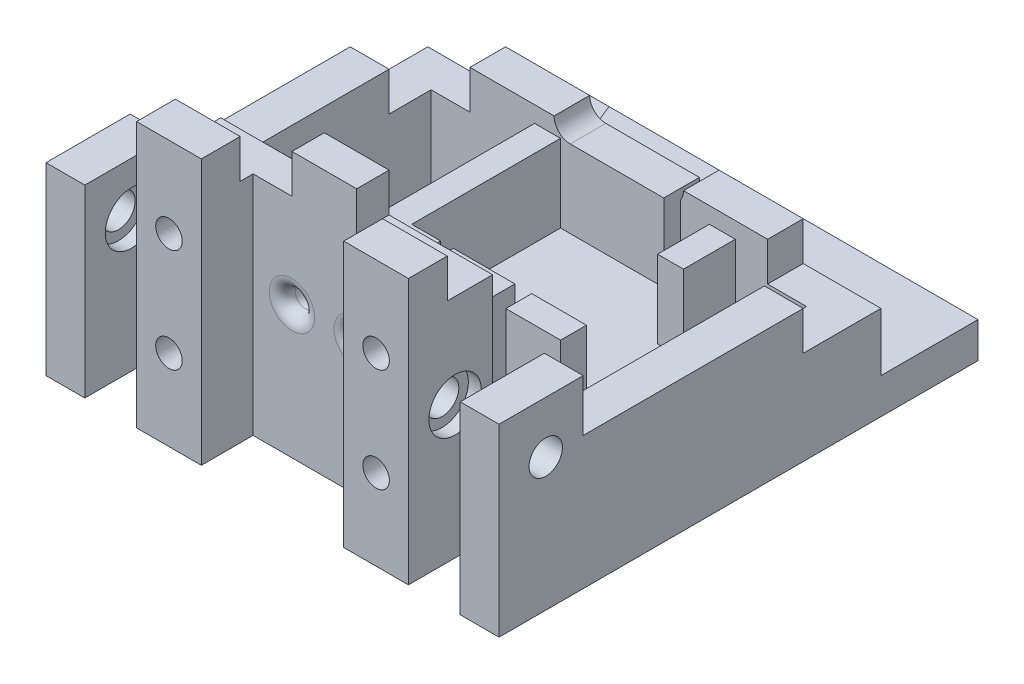
SolidWorks part; units mm, degrees
material "PBT General Purpose"
ref_plane "Front Plane" through (0, 0, 0) normal (0, 0, 1) x (1, 0, 0)
ref_plane "Top Plane" through (0, 0, 0) normal (0, 1, 0) x (1, 0, 0)
ref_plane "Right Plane" through (0, 0, 0) normal (1, 0, 0) x (0, 0, -1)
sketch "Sketch1" plane through (0, 0, 0) normal (0, 1, 0) x (1, 0, 0)
  line L0 (-29, 24) -> (-29, -29.5)
  line L1 (-35, 29.5) -> (35, 29.5)
  line L2 (-35, 29.5) -> (-35, -29.5)
  line L3 (-35, -29.5) -> (-29, -29.5)
  line L4 (35, 29.5) -> (35, -29.5)
  line L6 (29, 24) -> (29, -29.5)
  line L8 (-29, -23.5) -> (29, -23.5) construction
  line L9 (-29, 23.5) -> (-29, -23.5) construction
  line L10 (29, 23.5) -> (29, -23.5) construction
  line L11 (29, -29.5) -> (35, -29.5)
  line L12 (-35, -29.5) -> (35, -29.5) construction
  line L13 (-29, 23.5) -> (29, 23.5) construction
  line L14 (-29, 24) -> (29, 24)
  point P4 (0, 29.5)
  point P5 (35, 0)
  dimension "D1" = 70
  dimension "D2" = 59
  dimension "D4" = 5.5
  dimension "D3" = 6
extrude "Boss-Extrude1" add sketch "Sketch1" against normal blind 20.5
sketch "Sketch5" plane through (0, -20.5, 0) normal (0, 1, 0) x (1, 0, 0)
  line L0 (-29, 24) -> (29, 24) construction
  line L1 (-9, 24) -> (14, 24)
  line L2 (-9, 24) -> (-9, 1)
  line L3 (-9, 1) -> (14, 1)
  line L4 (14, 24) -> (14, 1)
  line L6 (29, -29.5) -> (29, 24) construction
  dimension "D1" = 23
  dimension "D2" = 23
  dimension "D4" = 15
extrude "Boss-Extrude3" add sketch "Sketch5" along normal offset from surface (6 mm away) 14.5 separate body up to face at (0, 0, 1.375)
sketch "Sketch16" plane through (0, -20.5, 0) normal (0, -1, 0) x (1, 0, 0)
  line L1 (18, -24) -> (14, -24)
  line L2 (18, -24) -> (18, 3)
  line L3 (18, 3) -> (-13, 3)
  line L4 (-9, -24) -> (14, -24)
  line L5 (-9, -1) -> (-9, -24)
  line L6 (14, -1) -> (-9, -1)
  line L7 (14, -24) -> (14, -1)
  line L9 (-9, -1) -> (-9, -24)
  line L10 (14, -1) -> (-9, -1)
  line L11 (14, -24) -> (14, -1)
  line L12 (-13, -24) -> (-13, 3)
  line L13 (-9, -24) -> (-13, -24)
  line L14 (-29, -24) -> (29, -24) construction
  dimension "D2" = 4
  dimension "D3" = 4
  dimension "D4" = 4
  dimension "D1" = 0
extrude "Boss-Extrude6" add sketch "Sketch16" against normal offset from surface (18 mm away) 12 up to face at (2.5, -14.5, -12.5) offset beyond the face yes
sketch "Sketch18" plane through (0, 0, 0) normal (0, 1, 0) x (1, 0, 0)
  line L6 (18, -3) -> (-13, -3) construction
  line L7 (6.95, -3) -> (9.55, -3)
  line L8 (6.95, -3) -> (6.95, 1)
  line L9 (6.95, 1) -> (9.55, 1)
  line L10 (9.55, -3) -> (9.55, 1)
  line L11 (-9, 1) -> (14, 1) construction
  line L12 (14, 1) -> (-9, 1) construction
  line L13 (-4.55, -3) -> (-2.55, -3)
  line L14 (-4.55, -3) -> (-4.55, 1)
  line L15 (-4.55, 1) -> (-2.55, 1)
  line L16 (-2.55, -3) -> (-2.55, 1)
  line L17 (18, 24) -> (18, -3) construction
  line L18 (14, 1) -> (18, 1)
  line L19 (14, 1) -> (14, 16)
  line L20 (14, 16) -> (18, 16)
  line L21 (18, 1) -> (18, 16)
  line L28 (9.55, 24) -> (9.55, 29.5)
  line L29 (9.55, 29.5) -> (6.95, 29.5)
  line L30 (6.95, 24) -> (6.95, 29.5)
  line L31 (35, 29.5) -> (-35, 29.5) construction
  line L32 (6.95, 24) -> (9.55, 24)
  line L33 (-29, 24) -> (29, 24) construction
  dimension "D1" = 15
  dimension "D2" = 4.45
  dimension "D3" = 2.6
  dimension "D4" = 9.5
  dimension "D5" = 2
extrude "Cut-Extrude10" cut sketch "Sketch18" against normal up to surface (14.5 mm away) up to face at (2.5, -14.5, -12.5)
sketch "gear_alignment_sketch" plane through (35, 0, 0) normal (1, 0, 0) x (0, 0, -1)
  line L0 (7, 0) -> (7, -20.5) construction
  line L1 (-29.5, 0) -> (29.5, 0) construction
  line L2 (-29.5, -20.5) -> (29.5, -20.5) construction
  line L3 (-992.2945, 0) -> (49007.7055, 0) construction
  line L5 (-29.5, 0) -> (29.5, 0) construction
  line L7 (-22.2916, 0) -> (7, -8.5) construction
  line L8 (16, -14.5) -> (24, -14.5) construction
  point P7 (-22.2916, 0)
  point P10 (7, -8.5)
  dimension "D1" = 6
  dimension "D3" = 30.5
  dimension "D2" = 6
sketch "Sketch8" plane through (0, 0, 0) normal (0, 1, 0) x (1, 0, 0)
  line L1 (35, -16.5) -> (29, -16.5)
  line L2 (35, -16.5) -> (35, -29.5)
  line L3 (35, -29.5) -> (29, -29.5)
  line L4 (29, -16.5) -> (29, -29.5)
  line L9 (29, 24) -> (29, -29.5) construction
  line L10 (35, -29.5) -> (35, 29.5) construction
  dimension "D1" = 13
extrude "Boss-Extrude4" add sketch "Sketch8" along normal blind 8
sketch "Sketch7" plane through (35, 0, 0) normal (1, 0, 0) x (0, 0, -1)
  circle A0 centre (-22.2916, 0) radius 2.575
  dimension "D1" = 5.15
extrude "x" cut sketch "Sketch7" against normal up to next (6 mm away)
sketch "Sketch9" plane through (29, 0, 0) normal (1, 0, 0) x (0, 0, -1)
  circle A0 centre (-22.2916, 0) radius 4.05
  dimension "D1" = 8.1
extrude "Cut-Extrude4" cut sketch "Sketch9" along normal blind 2
sketch "Sketch10" plane through (0, -20.5, 0) normal (0, -1, 0) x (1, 0, 0)
  line L1 (0, 16.5) -> (29, 16.5)
  line L3 (0, 29.5) -> (29, 29.5)
  line L4 (29, 16.5) -> (29, 29.5)
  line L5 (29, 29.5) -> (29, -24) construction
  line L6 (35, 16.5) -> (29, 16.5) construction
  line L7 (29, 29.5) -> (35, 29.5) construction
  line L8 (0, -1000) -> (0, 49000) construction
  line L9 (0, 16.5) -> (0, 29.5)
extrude "Boss-Extrude5" add sketch "Sketch10" against normal up to surface (28.5 mm away) up to face at (32, 8, 23)
sketch "Sketch12" plane through (0, 8, 0) normal (0, 1, 0) x (1, 0, 0)
  line L0 (0, -29.5) -> (35, -29.5) construction
  line L1 (29, -16.5) -> (21, -16.5)
  line L2 (29, -16.5) -> (29, -29.5)
  line L3 (29, -29.5) -> (21, -29.5)
  line L4 (21, -16.5) -> (21, -29.5)
  dimension "D1" = 8
extrude "Cut-Extrude6" cut sketch "Sketch12" against normal blind 24
sketch "Sketch13" plane through (21, 0, 0) normal (1, 0, 0) x (0, 0, -1)
  circle A0 centre (-22.2916, 0) radius 2.575
  circle A1 centre (-22.2916, 0) radius 2.575 construction
extrude "Cut-Extrude7" cut sketch "Sketch13" against normal blind 6
sketch "Sketch14" plane through (21, 0, 0) normal (1, 0, 0) x (0, 0, -1)
  circle A0 centre (-22.2916, 0) radius 4.05
  circle A1 centre (-22.2916, 0) radius 4.05 construction
extrude "Cut-Extrude8" cut sketch "Sketch14" against normal blind 2
mirror "Mirror1" about plane through (0, 0, 0) normal (1, 0, 0) of "Cut-Extrude8", "Cut-Extrude7", "Cut-Extrude6", "Boss-Extrude5", "Boss-Extrude4", "x", "Cut-Extrude4"
sketch "Sketch35" plane through (0, 0, 29.5) normal (0, 0, 1) x (1, 0, 0)
  line L0 (-5, 0) -> (5, 0) construction
  line L1 (-21, 8) -> (21, 8) construction
  circle A2 centre (-5, 0) radius 1.5
  circle A3 centre (5, 0) radius 1.5
  point P3 (0, 0)
  point P16 (0, 8)
  dimension "D1" = 3
  dimension "D2" = 3
  dimension "D3" = 10
extrude "Cut-Extrude21" cut sketch "Sketch35" against normal up to next
sketch "Sketch36" plane through (0, 8, 0) normal (0, 1, 0) x (1, 0, 0)
  line L0 (5, -29.5) -> (5, -16.5) construction
  line L1 (-21, -29.5) -> (21, -29.5) construction
  line L2 (21, -16.5) -> (-21, -16.5) construction
  line L3 (0, -29.5) -> (0, -16.5) construction
  line L4 (3.5, -29.5) -> (6.5, -29.5) construction
  line L5 (-5, -29.5) -> (5, -29.5)
  line L6 (5, -29.5) -> (11, -29.5)
  line L7 (11, -21.5) -> (11, -29.5)
  line L8 (21, -16.5) -> (21, -29.5) construction
  line L9 (11, -21.5) -> (-11, -21.5)
  line L10 (-11, -21.5) -> (-11, -29.5)
  line L11 (-5, -29.5) -> (-11, -29.5)
  point P18 (0, -21.5)
  dimension "D1" = 10
  dimension "D2" = 5
extrude "Cut-Extrude22" cut sketch "Sketch36" against normal up to next
fillet "Fillet1" radius 2 4 edges at (6.5, 0, 16.5) (-3.5, 0, 16.5) (3.5, 0, 21.5) (-6.5, 0, 21.5)
sketch "Sketch37" plane through (0, 8, 0) normal (0, 1, 0) x (1, 0, 0)
  line L8 (-11, -21.5) -> (11, -21.5)
  line L9 (11, -21.5) -> (11, -29.5)
  line L10 (11, -29.5) -> (21, -29.5)
  line L11 (21, -29.5) -> (21, -16.5)
  line L12 (21, -16.5) -> (-21, -16.5)
  line L13 (-21, -16.5) -> (-21, -29.5)
  line L14 (-21, -29.5) -> (-11, -29.5)
  line L15 (-11, -29.5) -> (-11, -21.5)
  line L16 (-11, -21.5) -> (11, -21.5)
  line L17 (11, -21.5) -> (11, -29.5)
  line L18 (11, -29.5) -> (21, -29.5)
  line L19 (21, -29.5) -> (21, -16.5)
  line L20 (21, -16.5) -> (-21, -16.5)
  line L21 (-21, -16.5) -> (-21, -29.5)
  line L22 (-21, -29.5) -> (-11, -29.5)
  line L23 (-11, -29.5) -> (-11, -21.5)
  dimension "D1" = 0
extrude "Boss-Extrude7" add sketch "Sketch37" along normal blind 12.5
sketch "Sketch34" plane through (0, 0, 29.5) normal (0, 0, 1) x (1, 0, 0)
  line L2 (0, -20.5) -> (0, 8) construction
  line L8 (11, 8) -> (21, 8) construction
  line L9 (11, -20.5) -> (35, -20.5) construction
  circle A0 centre (16, -8) radius 2.05
  circle A4 centre (16, 8) radius 2.05
  circle A5 centre (-16, 8) radius 2.05
  circle A6 centre (-16, -8) radius 2.05
  point P8 (0, -20.5)
  dimension "D1" = 8
  dimension "D2" = 4.1
  dimension "D4" = 4.1
  dimension "D3" = 16
  dimension "D5" = 16
extrude "Cut-Extrude20" cut sketch "Sketch34" against normal blind 10
sketch "Sketch38" plane through (0, 0, -29.5) normal (0, 0, -1) x (-1, 0, 0)
  line L1 (-35, -20.5) -> (35, -20.5)
  line L2 (-35, -20.5) -> (-35, -15)
  line L3 (-35, -15) -> (35, -15)
  line L4 (35, -20.5) -> (35, -15)
  line L5 (35, -20.5) -> (35, 0) construction
  line L6 (-6.95, 0) -> (35, 0) construction
  dimension "D1" = 15
extrude "Boss-Extrude8" add sketch "Sketch38" along normal blind 15
sketch "Sketch39" plane through (0, -15, 0) normal (0, 1, 0) x (1, 0, 0)
  line L0 (35, 37) -> (-35, 37) construction
  line L1 (35, 44.5) -> (35, 29.5) construction
  line L2 (-35, 44.5) -> (-35, 29.5) construction
  line L3 (0, 29.5) -> (0, 37) construction
  line L4 (-35, 29.5) -> (35, 29.5) construction
  line L5 (-35, 44.5) -> (35, 44.5) construction
  line L6 (11.5, 29.5) -> (14.5, 37)
  line L14 (14.5, 37) -> (-14.5, 37)
  line L15 (11.5, 29.5) -> (-11.5, 29.5)
  line L16 (-11.5, 29.5) -> (-14.5, 37)
  dimension "D1" = 23
  dimension "D2" = 3
  dimension "D3" = 7.5
extrude "Boss-Extrude9" add sketch "Sketch39" along normal blind 7.5
sketch "Sketch40" plane through (0, 0, -29.5) normal (0, 0, -1) x (-1, 0, 0)
  line L0 (-6.95, 0) -> (35, 0) construction
  line L1 (-7.5, 0) -> (7.5, 0) construction
  line L2 (-7.5, 2.5) -> (7.5, 2.5)
  line L3 (-7.5, -2.5) -> (7.5, -2.5)
  arc A0 (-7.5, 2.5) -> (-7.5, -2.5) centre (-7.5, 0) ccw
  arc A1 (7.5, -2.5) -> (7.5, 2.5) centre (7.5, 0) ccw
  point P4 (0, 0)
  dimension "D1" = 2.5
  dimension "D2" = 15
extrude "Cut-Extrude23" cut sketch "Sketch40" against normal up to next
sketch "Sketch41" plane through (29, 0, 0) normal (-1, 0, 0) x (0, 0, 1)
  line L0 (-24, -20.5) -> (16.5, -20.5) construction
  line L1 (-0.5, -20.5) -> (9.5, -20.5)
  line L2 (-0.5, -20.5) -> (-0.5, -18.5)
  line L3 (2.5, -15.5) -> (6.5, -15.5)
  line L4 (9.5, -20.5) -> (9.5, -17.5)
  line L5 (29.5, -16) -> (29.5, 8) construction
  line L6 (-0.5, -18.5) -> (2.5, -15.5)
  line L7 (6.5, -15.5) -> (9.5, -17.5)
  point P1 (9.5, -15.5)
  point P2 (-0.5, -15.5)
  dimension "D1" = 30
  dimension "D2" = 10
  dimension "D3" = 5
  dimension "D4" = 3
  dimension "D7" = 2
extrude "Boss-Extrude10" add sketch "Sketch41" along normal up to surface (58 mm away) up to face at (-29, -7.125, 9.625)
sketch "Sketch42" plane through (0, 0, 29.5) normal (0, 0, 1) x (1, 0, 0)
  line L0 (11, -20.5) -> (35, -20.5) construction
  line L1 (21, -16) -> (29, -16)
  line L2 (21, -16) -> (21, -20.5)
  line L3 (21, -20.5) -> (29, -20.5)
  line L4 (29, -16) -> (29, -20.5)
  line L5 (29, -16) -> (29, 8) construction
  line L6 (-35, -20.5) -> (-11, -20.5) construction
  line L7 (-29, -16) -> (-21, -16)
  line L8 (-29, -16) -> (-29, -20.5)
  line L9 (-29, -20.5) -> (-21, -20.5)
  line L10 (-21, -16) -> (-21, -20.5)
  line L11 (-21, -16) -> (-21, 20.5) construction
extrude "Cut-Extrude24" cut sketch "Sketch42" against normal up to next
sketch "Sketch43" plane through (35, 0, 0) normal (1, 0, 0) x (0, 0, -1)
  line L0 (-9.5, -20.5) -> (-9.5, -15.5)
  line L1 (-9.5, -15.5) -> (0.5, -15.5)
  line L2 (0.5, -15.5) -> (0.5, -20.5)
  line L3 (0.5, -20.5) -> (-9.5, -20.5)
  point P2 (0, 0)
  point P5 (0, 0)
  point P8 (0, 0)
  point P10 (0, 0)
extrude "Boss-Extrude11" add sketch "Sketch43" against normal up to surface (42 mm away) from surface at -14 starting at face at (21, 0, 18.2416)
sketch "Sketch44" plane through (0, 0, 9.5) normal (0, 0, 1) x (1, 0, 0)
  line L0 (-29, -20.5) -> (29, -20.5) construction
  line L1 (-21, -15.5) -> (21, -15.5)
  line L2 (-21, -15.5) -> (-21, -20.5)
  line L3 (-21, -20.5) -> (21, -20.5)
  line L4 (21, -15.5) -> (21, -20.5)
  line L5 (-21, -17.5) -> (-21, -15.5) construction
  point P4 (0, 0)
  point P5 (-20.6221, -20.1577)
  point P7 (0, 0)
extrude "Boss-Extrude12" add sketch "Sketch44" along normal up to next
sketch "Sketch45" plane through (0, 0, 0) normal (0, 1, 0) x (1, 0, 0)
  line L1 (35, 29.5) -> (23, 29.5)
  line L2 (35, 29.5) -> (35, 17.5)
  line L3 (35, 17.5) -> (23, 17.5)
  line L4 (23, 29.5) -> (23, 17.5)
  line L5 (-35, 29.5) -> (-23, 29.5)
  line L6 (-35, 29.5) -> (-35, 17.5)
  line L7 (-35, 17.5) -> (-23, 17.5)
  line L8 (-23, 29.5) -> (-23, 17.5)
  dimension "D1" = 12
  dimension "D2" = 12
  dimension "D3" = 12
  dimension "D4" = 12
extrude "Cut-Extrude25" cut sketch "Sketch45" against normal blind 6
sketch "Sketch46" plane through (0, 20.5, 0) normal (0, 1, 0) x (1, 0, 0)
  line L0 (-5, -21.5) -> (-5, -16.5)
  line L1 (5, -21.5) -> (5, -16.5)
  line L2 (-5, -16.5) -> (-21, -16.5)
  line L3 (5, -21.5) -> (11, -21.5)
  line L4 (-11, -21.5) -> (11, -21.5) construction
  line L5 (11, -23.5) -> (21, -23.5)
  line L6 (-11, -23.5) -> (-21, -23.5)
  line L7 (11, -29.5) -> (21, -29.5) construction
  line L8 (-11, -29.5) -> (-11, -21.5)
  line L9 (-11, -21.5) -> (11, -21.5)
  line L10 (11, -21.5) -> (11, -29.5)
  line L11 (11, -29.5) -> (21, -29.5)
  line L12 (21, -29.5) -> (21, -16.5)
  line L13 (21, -16.5) -> (-21, -16.5)
  line L14 (-21, -16.5) -> (-21, -29.5)
  line L15 (-21, -29.5) -> (-11, -29.5)
  line L16 (-11, -23.5) -> (-11, -21.5)
  line L17 (-11, -21.5) -> (-5, -21.5)
  line L18 (11, -21.5) -> (11, -23.5)
  line L20 (21, -23.5) -> (21, -16.5)
  line L21 (21, -16.5) -> (5, -16.5)
  line L22 (-21, -16.5) -> (-21, -23.5)
  point P14 (0, -21.5)
  dimension "D2" = 5
  dimension "D3" = 10
  dimension "D4" = 6
  dimension "D1" = 0
extrude "Cut-Extrude26" cut sketch "Sketch46" against normal blind 6
equation "\"bushing_hole_outer_diameter\"= 8.1mm"
equation "\"bushing_hole_inner_diameter\"= 5.15mm"
equation "\"bushing_flange_depth\"= 2mm"
equation "\"D1@Boss-Extrude3\"=12 + 2.5"
equation "\"gear_spacing\"= 30.5mm"
equation "\"D3@gear_alignment_sketch\" = \"gear_spacing\""
equation "\"D1@Sketch7\"=\"bushing_hole_inner_diameter\""
equation "\"D1@Sketch9\"=\"bushing_hole_outer_diameter\""
equation "\"D1@Cut-Extrude4\"=\"bushing_flange_depth\""
equation "\"D1@Cut-Extrude8\"=\"bushing_flange_depth\""
equation "\"body_height\"= 41mm"
equation "\"D1@Boss-Extrude1\"= \"body_height\" / 2"
